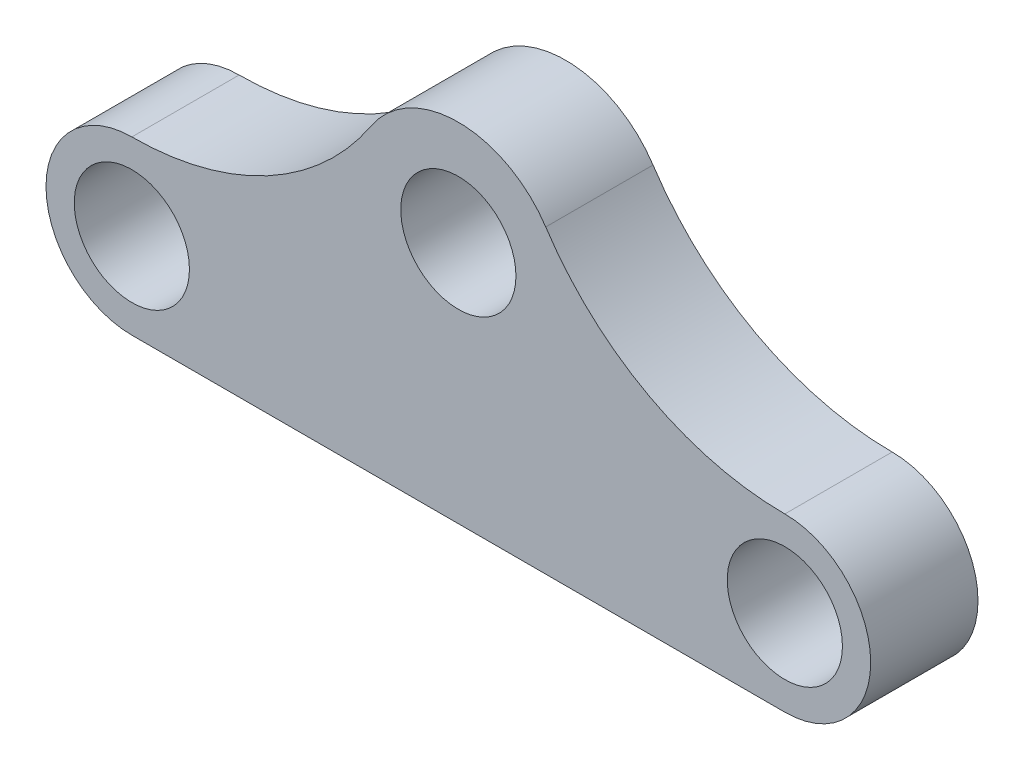
SolidWorks part; units mm, degrees
material "ABS"
ref_plane "Front Plane" through (0, 0, 0) normal (0, 0, 1) x (1, 0, 0)
ref_plane "Top Plane" through (0, 0, 0) normal (0, 1, 0) x (1, 0, 0)
ref_plane "Right Plane" through (0, 0, 0) normal (1, 0, 0) x (0, 0, -1)
sketch "Sketch1" plane through (0, 0, 0) normal (0, 0, 1) x (1, 0, 0)
  line L0 (0, 0) -> (45.64, 0) construction
  line L1 (0, 6) -> (45.64, 6)
  line L2 (0, -6) -> (45.64, -6)
  line L3 (0, 6) -> (45.64, 6)
  arc A0 (0, 6) -> (0, -6) centre (0, 0) ccw
  arc A1 (45.64, -6) -> (45.64, 6) centre (45.64, 0) ccw
  circle A2 centre (0, 0) radius 4.025
  circle A3 centre (45.64, 0) radius 4.025
  arc A4 (0, 6) -> (16.7128, 15.0144) centre (0, 26) ccw
  arc A5 (45.64, 6) -> (28.9272, 15.0144) centre (45.64, 26) cw
  arc A6 (16.7128, 15.0144) -> (28.9272, 15.0144) centre (22.82, 11) cw
  circle A7 centre (22.82, 11) radius 4.025
  point P3 (22.82, 0)
  point P18 (7, 10.5)
  point P21 (8.9151, 8.97)
  point P22 (29.9231, 11.1316)
  point P23 (0, 0)
  dimension "D1" = 8.05
  dimension "D3" = 6
  dimension "D4" = 20
  dimension "D2" = 45.64
  dimension "D5" = 5
extrude "Boss-Extrude1" add sketch "Sketch1" along normal blind 7.5
